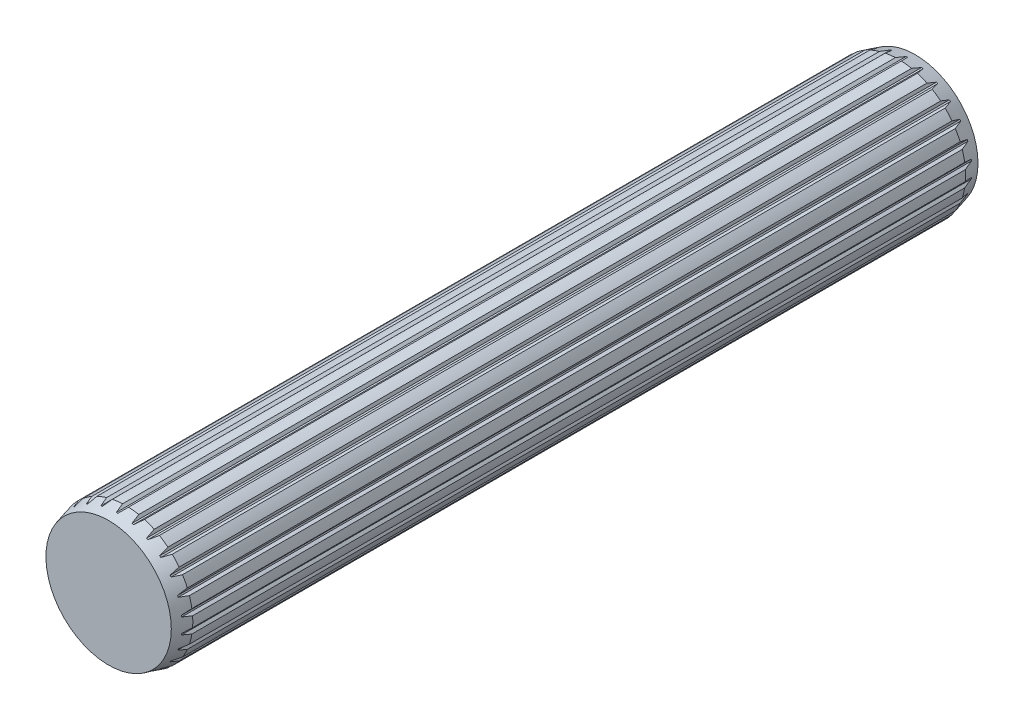
SolidWorks part; units mm, degrees
ref_plane "Front Plane" through (0, 0, 0) normal (0, 0, 1) x (1, 0, 0)
ref_plane "Top Plane" through (0, 0, 0) normal (0, 1, 0) x (1, 0, 0)
ref_plane "Right Plane" through (0, 0, 0) normal (1, 0, 0) x (0, 0, -1)
sketch "Sketch1" plane through (0, 0, 0) normal (1, 0, 0) x (0, 0, -1)
  line L0 (-19.05, 0) -> (19.05, 0)
  dimension "Length" = 38.1
sketch "Sketch2" plane through (0, 0, 0) normal (0, 0, 1) x (1, 0, 0)
  circle A1 centre (0, 0) radius 3.175
  point P4 (0, -3.175)
  dimension "Diameter" = 6.35
sketch "Sketch3" plane through (0, 0, 0) normal (1, 0, 0) x (0, 0, -1)
  line L0 (-19.05, 0) -> (-19.05, 2.9606)
  line L1 (-19.05, 2.9606) -> (-18.25, 3.175)
  line L2 (-18.25, 3.175) -> (18.25, 3.175)
  line L5 (19.05, 0) -> (-19.05, 0)
  line L6 (-19.05, 0) -> (19.05, 0) construction
  line L7 (-19.05, 0) -> (19.05, 0) construction
  line L8 (18.25, 3.175) -> (19.05, 2.9606)
  line L9 (19.05, 2.9606) -> (19.05, 0)
  point P0 (0, 3.175)
  point P2 (-9.525, 0)
  point P3 (-19.05, -3.175)
  point P5 (9.525, 0)
  dimension "Point Height" = 0.8
  dimension "D1" = 15
  dimension "D2" = 9.525
  dimension "D3" = 9.525
revolve "Revolve1" add sketch "Sketch3" angle 360 about L0
sketch "Sketch5" plane through (0, 0, 0) normal (0, 0, 1) x (1, 0, 0)
  line L0 (0, 3.175) -> (0, 2.9606) construction
  line L3 (0.1429, 3.175) -> (-0.1429, 3.175)
  line L4 (-0.0357, 3.0678) -> (0.0357, 3.0678)
  line L5 (-0.1429, 3.175) -> (-0.0715, 3.175) construction
  line L6 (-0.0715, 3.175) -> (0, 3.175) construction
  line L7 (-0.1429, 3.175) -> (-0.0357, 3.0678)
  line L8 (0.0357, 3.0678) -> (0.1429, 3.175)
  circle A0 centre (0, 0) radius 3.175 construction
  circle A2 centre (0, 0) radius 2.9606 construction
  point P0 (0, 3.0678)
extrude "Cut-Extrude1" cut sketch "Sketch5" along normal through all both and the other way through all
pattern_circular "CirPattern1" count 26 over 360 about axis through (0, 0, 0) along (0, 0, 1) of "Cut-Extrude1"
equation "\"Point Height@Sketch3\"=\"Length@Sketch1\"*.066"
equation "\"D1@CirPattern1\"=( \"Diameter@Sketch2\" * pi )  * 33"
equation "\"D2@Sketch3\"=\"Diameter@Sketch2\"*1.5"
equation "\"D3@Sketch3\"=\"D2@Sketch3\""
